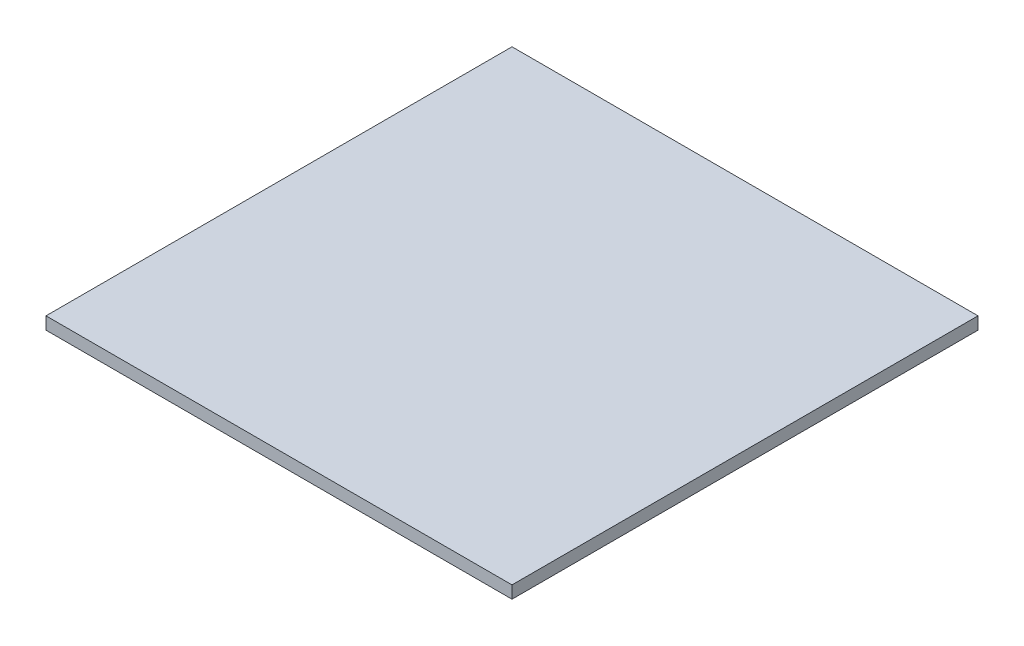
SolidWorks part; units mm, degrees
ref_plane "Front Plane" through (0, 0, 0) normal (0, 0, 1) x (1, 0, 0)
ref_plane "Top Plane" through (0, 0, 0) normal (0, 1, 0) x (1, 0, 0)
ref_plane "Right Plane" through (0, 0, 0) normal (1, 0, 0) x (0, 0, -1)
sketch "Sketch1" plane through (0, 0, 0) normal (0, 1, 0) x (1, 0, 0)
  line L1 (0, 0) -> (150, 0)
  line L2 (0, 0) -> (0, 150)
  line L3 (0, 150) -> (150, 150)
  line L4 (150, 0) -> (150, 150)
  dimension "D1" = 150
  dimension "D2" = 150
extrude "Boss-Extrude1" add sketch "Sketch1" along normal blind 4
